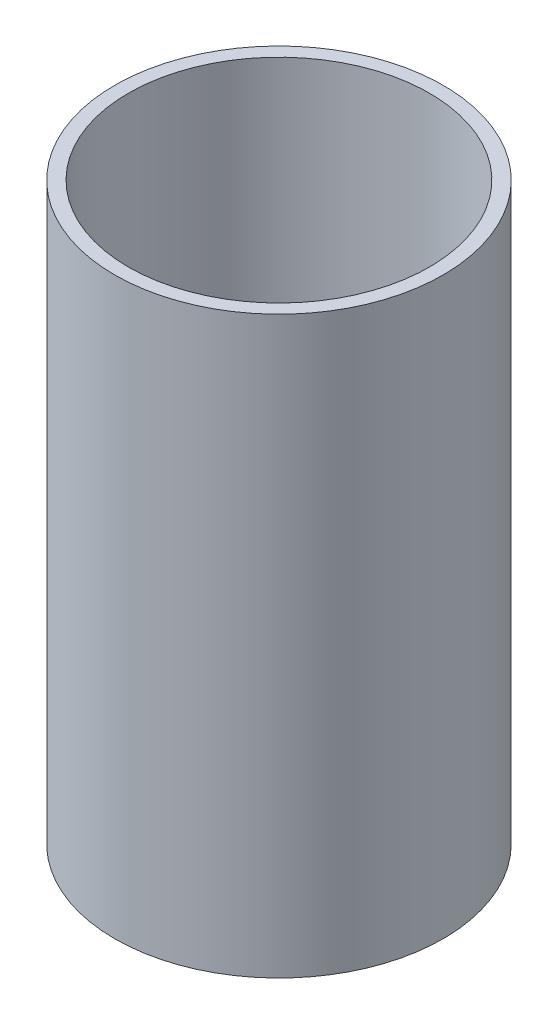
SolidWorks part; units mm, degrees
ref_plane "Front Plane" through (0, 0, 0) normal (0, 0, 1) x (1, 0, 0)
ref_plane "Top Plane" through (0, 0, 0) normal (0, 1, 0) x (1, 0, 0)
ref_plane "Right Plane" through (0, 0, 0) normal (1, 0, 0) x (0, 0, -1)
sketch "Sketch1" plane through (0, 0, 0) normal (0, 1, 0) x (1, 0, 0)
  circle A0 centre (0, 0) radius 11
  circle A1 centre (0, 0) radius 12
  dimension "D1" = 24
  dimension "D2" = 22
extrude "Boss-Extrude1" add sketch "Sketch1" along normal mid plane 42
